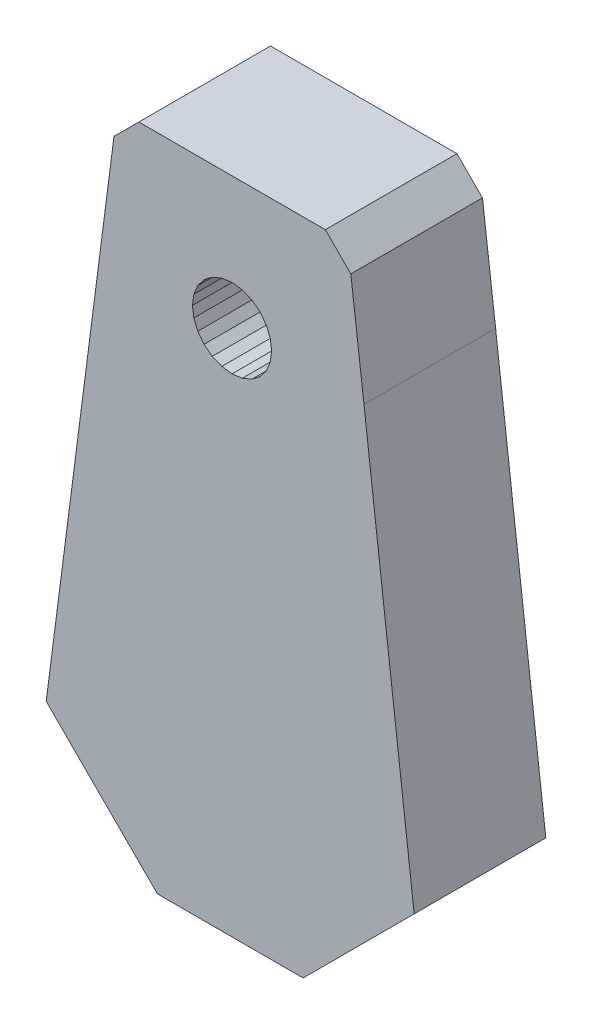
SolidWorks part; units mm, degrees
material "Maple"
ref_plane "Front Plane" through (0, 0, 0) normal (0, 0, 1) x (1, 0, 0)
ref_plane "Top Plane" through (0, 0, 0) normal (0, 1, 0) x (1, 0, 0)
ref_plane "Right Plane" through (0, 0, 0) normal (1, 0, 0) x (0, 0, -1)
sketch "Sketch1" plane through (0, 0, 0) normal (0, 0, 1) x (1, 0, 0)
  line L6300 (480.3342, 258.1103) -> (479.7354, 262.9604)
  line L6301 (482.6222, 239.1401) -> (480.3342, 258.1103)
  line L6302 (470.9174, 234.0772) -> (477.5594, 234.0772)
  line L6303 (465.8493, 239.1454) -> (470.9174, 234.0772)
  line L6304 (477.5594, 234.0772) -> (482.6222, 239.1401)
  line L6305 (468.94, 262.9917) -> (470.072, 264.1238)
  line L6306 (478.572, 264.1238) -> (470.072, 264.1238)
  line L6307 (478.572, 264.1238) -> (479.7354, 262.9604)
  line L6308 (475.8831, 259.0123) -> (476.0633, 258.5772)
  line L6309 (476.0633, 258.5772) -> (476.1248, 258.1103)
  line L6310 (476.1248, 258.1103) -> (476.0633, 257.6434)
  line L6311 (476.0633, 257.6434) -> (475.8831, 257.2083)
  line L6312 (475.8831, 257.2083) -> (475.5964, 256.8346)
  line L6313 (475.5964, 256.8346) -> (475.2228, 256.5479)
  line L6314 (475.2228, 256.5479) -> (474.7877, 256.3677)
  line L6315 (474.7877, 256.3677) -> (474.3208, 256.3062)
  line L6316 (474.3208, 256.3062) -> (473.8538, 256.3677)
  line L6317 (473.8538, 256.3677) -> (473.4187, 256.5479)
  line L6318 (473.4187, 256.5479) -> (473.0451, 256.8346)
  line L6319 (473.0451, 256.8346) -> (472.7584, 257.2083)
  line L6320 (472.7584, 257.2083) -> (472.5782, 257.6434)
  line L6321 (472.5782, 257.6434) -> (472.5167, 258.1103)
  line L6322 (472.5167, 258.1103) -> (472.5782, 258.5772)
  line L6323 (472.5782, 258.5772) -> (472.7584, 259.0123)
  line L6324 (472.7584, 259.0123) -> (473.0451, 259.3859)
  line L6325 (473.0451, 259.3859) -> (473.4187, 259.6726)
  line L6326 (473.4187, 259.6726) -> (473.8538, 259.8529)
  line L6327 (473.8538, 259.8529) -> (474.3208, 259.9143)
  line L6328 (474.3208, 259.9143) -> (474.7877, 259.8529)
  line L6329 (474.7877, 259.8529) -> (475.2228, 259.6726)
  line L6330 (475.2228, 259.6726) -> (475.5964, 259.3859)
  line L6331 (475.5964, 259.3859) -> (475.8831, 259.0123)
  line L8420 (465.8493, 239.1454) -> (468.94, 262.9917)
  line L9399 (473.286, 242.9485) -> (473.286, 242.6426)
  line L9400 (473.286, 242.6426) -> (473.3061, 242.5464)
  line L9401 (473.3061, 242.5464) -> (473.3664, 242.4576)
  line L9402 (473.3664, 242.4576) -> (473.6075, 242.3022)
  line L9403 (473.6075, 242.3022) -> (473.9689, 242.1969)
  line L9404 (473.9689, 242.1969) -> (474.4099, 242.1618)
  line L9405 (474.4099, 242.1618) -> (474.8509, 242.1969)
  line L9406 (474.8509, 242.1969) -> (475.2123, 242.3022)
  line L9407 (475.2123, 242.3022) -> (475.4534, 242.4576)
  line L9408 (475.4534, 242.4576) -> (475.5137, 242.5464)
  line L9409 (475.5137, 242.5464) -> (475.5338, 242.6426)
  line L9410 (475.5338, 242.6426) -> (475.5338, 246.4514)
  line L9411 (475.5338, 246.4514) -> (475.5338, 242.6426)
  line L9412 (475.5338, 242.6426) -> (475.5137, 242.5464)
  line L9413 (475.5137, 242.5464) -> (475.4534, 242.4576)
  line L9414 (475.4534, 242.4576) -> (475.2123, 242.3022)
  line L9415 (475.2123, 242.3022) -> (474.8509, 242.1969)
  line L9416 (474.8509, 242.1969) -> (474.4099, 242.1618)
  line L9417 (474.4099, 242.1618) -> (473.9689, 242.1969)
  line L9418 (473.9689, 242.1969) -> (473.6075, 242.3022)
  line L9419 (473.6075, 242.3022) -> (473.3664, 242.4576)
  line L9420 (473.3664, 242.4576) -> (473.3061, 242.5464)
  line L9421 (473.3061, 242.5464) -> (473.286, 242.6426)
  line L9422 (473.286, 242.6426) -> (473.286, 242.9485)
extrude "Boss-Extrude1" add sketch "Sketch1" along normal blind 6
